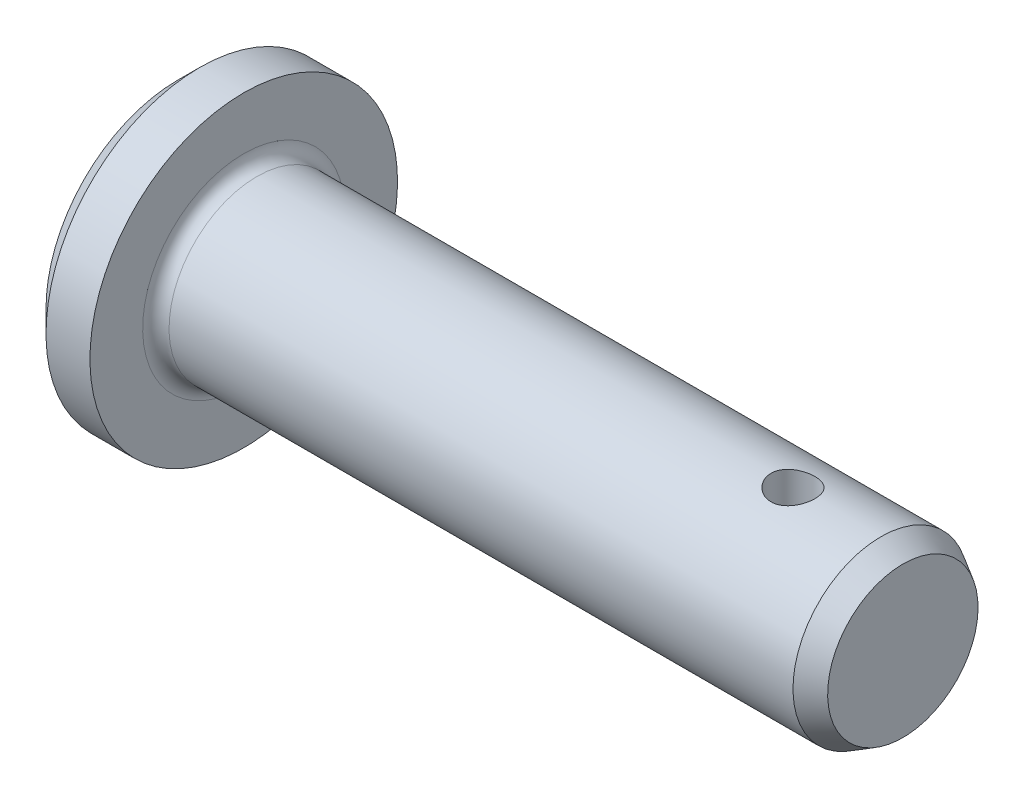
SolidWorks part; units mm, degrees
ref_plane "Ebene vorne" through (0, 0, 0) normal (0, 0, 1) x (1, 0, 0)
ref_plane "Ebene oben" through (0, 0, 0) normal (0, 1, 0) x (1, 0, 0)
ref_plane "Ebene rechts" through (0, 0, 0) normal (1, 0, 0) x (0, 0, -1)
sketch "Skizze1" plane through (0, 0, 0) normal (0, 0, 1) x (1, 0, 0)
  line L0 (-3, 0) -> (-3, 6)
  line L1 (7.7, 0) -> (-7.7, 0) construction
  line L2 (-2, 7) -> (0, 7)
  line L3 (0, -7.7) -> (0, 7.7) construction
  line L4 (0, 7) -> (0, 4)
  line L5 (0, 4) -> (29, 4)
  line L12 (30, 0) -> (-3, 0)
  line L13 (-2, 7) -> (-3, 6)
  line L18 (30, 3.4226) -> (30, 0)
  line L19 (30, 3.4226) -> (29, 4)
  dimension "D1" = 7
  dimension "D2" = 4
  dimension "D3" = 3
  dimension "D7" = 1
  dimension "D8" = 135
  dimension "D4" = 120
  dimension "D5" = 1
  dimension "D6" = 30
revolve "Rotation1" add sketch "Skizze1" angle 360 about L12
fillet "Verrundung1" radius 0.6 1 edges at (0, 4, 0)
sketch "Skizze2" plane through (0, 0, 0) normal (0, 1, 0) x (1, 0, 0)
  line L0 (-7.7, 0) -> (7.7, 0) construction
  line L1 (30, -3.4226) -> (30, 3.4226) construction
  circle A0 centre (25, 0) radius 1
  dimension "D1" = 2
  dimension "D2" = 5
extrude "Schnitt-Linear austragen1" cut sketch "Skizze2" against normal up to next and the other way up to next
equation "\"diameter\"= 8"
equation "\"length\"= 30"
equation "\"head_diameter\"= 14"
equation "\"head_thickness\"= 3"
equation "\"radius\"= 0.6"
equation "\"chamfer_height\"= 1"
equation "\"D2@Skizze1\"= \"diameter\" / 2"
equation "\"D1@Skizze1\"= \"head_diameter\" / 2"
equation "\"D3@Skizze1\"= \"head_thickness\""
equation "\"D1@Verrundung1\"= \"radius\""
equation "\"D7@Skizze1\"= \"chamfer_height\""
equation "\"hole_diameter\" = 2"
equation "\"hole_distance\"= 5"
equation "\"chamfer_height_30\"= 1"
equation "\"D5@Skizze1\"= \"chamfer_height_30\""
equation "\"D6@Skizze1\"= \"length\""
equation "\"D1@Skizze2\"= \"hole_diameter\""
equation "\"D2@Skizze2\"= \"hole_distance\""
